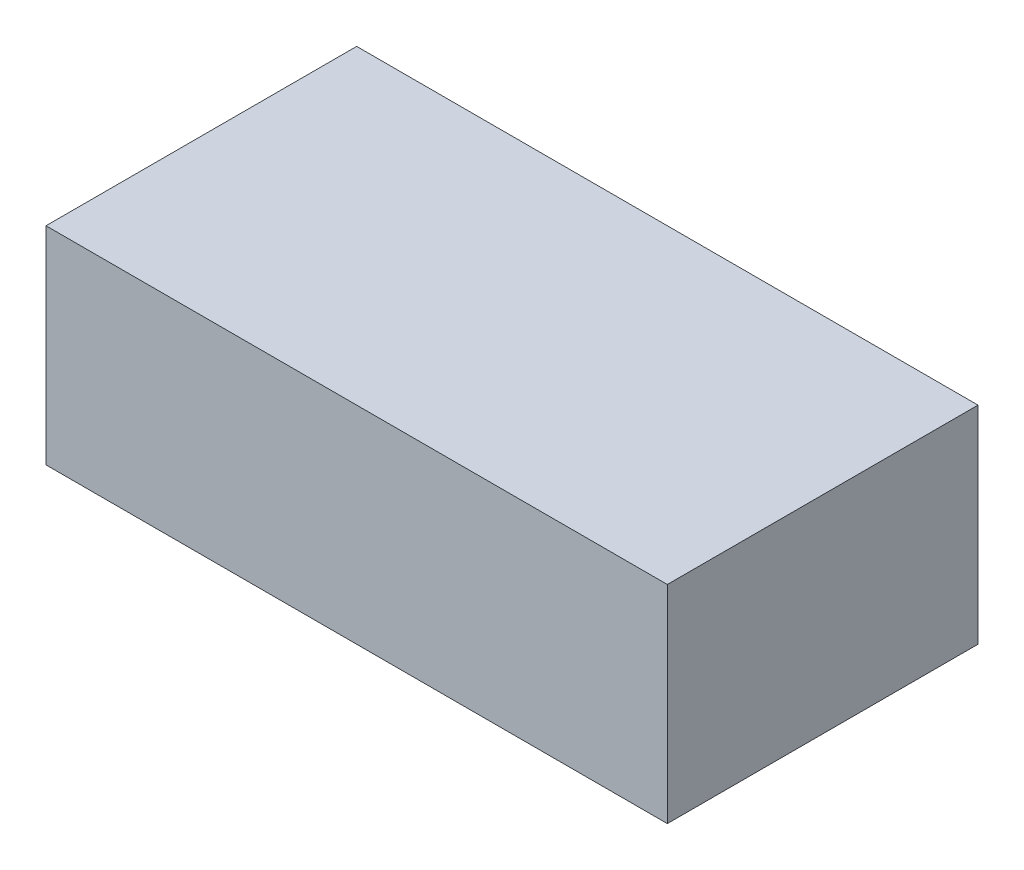
SolidWorks part; units mm, degrees
ref_plane "Front Plane" through (0, 0, 0) normal (0, 0, 1) x (1, 0, 0)
ref_plane "Top Plane" through (0, 0, 0) normal (0, 1, 0) x (1, 0, 0)
ref_plane "Right Plane" through (0, 0, 0) normal (1, 0, 0) x (0, 0, -1)
sketch "Sketch1" plane through (0, 0, 0) normal (0, 1, 0) x (1, 0, 0)
  line L1 (-30, -15) -> (30, -15)
  line L2 (-30, -15) -> (-30, 15)
  line L3 (-30, 15) -> (30, 15)
  line L4 (30, -15) -> (30, 15)
  line L5 (-30, -15) -> (30, 15) construction
  line L6 (-30, 15) -> (30, -15) construction
  point P0 (0, 0)
  dimension "D1" = 60
  dimension "D2" = 30
extrude "Boss-Extrude1" add sketch "Sketch1" along normal blind 20
